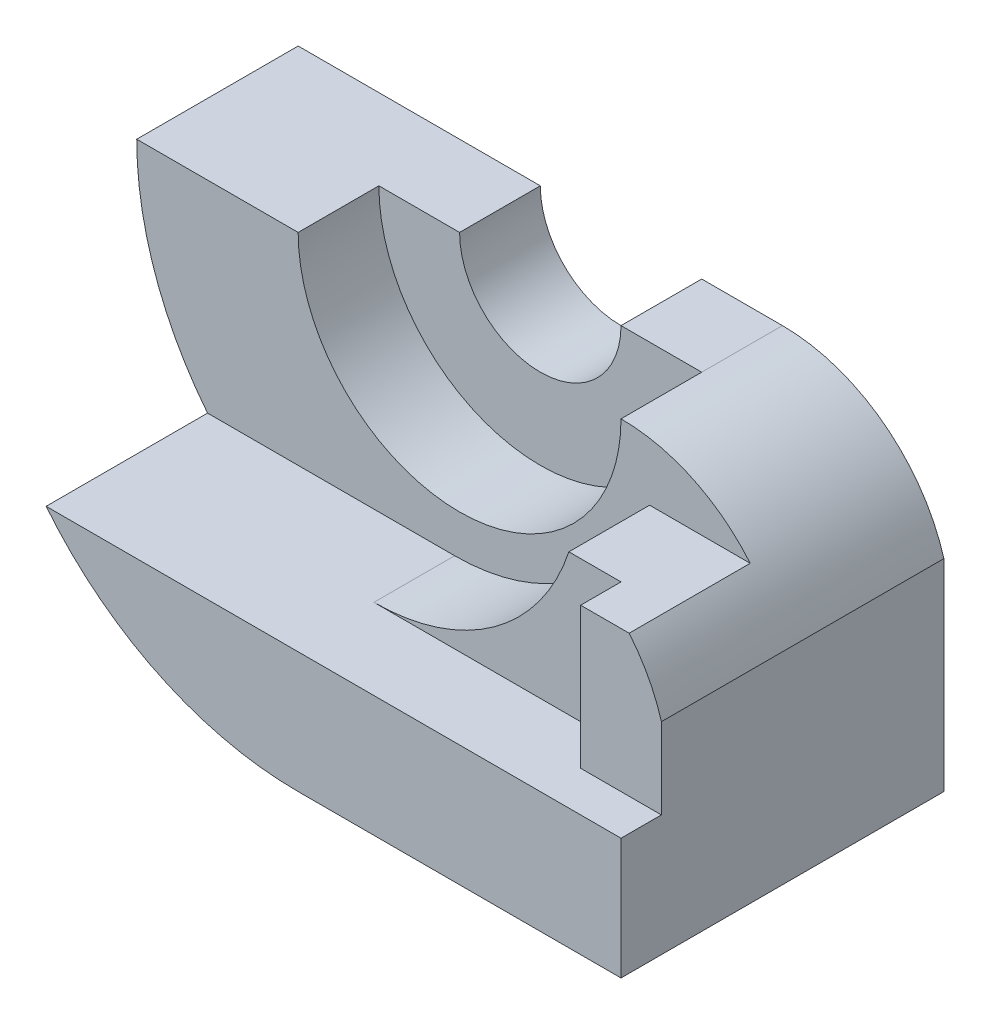
SolidWorks part; units mm, degrees
ref_plane "Front Plane" through (0, 0, 0) normal (0, 0, 1) x (1, 0, 0)
ref_plane "Top Plane" through (0, 0, 0) normal (0, 1, 0) x (1, 0, 0)
ref_plane "Right Plane" through (0, 0, 0) normal (1, 0, 0) x (0, 0, -1)
sketch "Sketch1" plane through (0, 0, 0) normal (0, 0, 1) x (1, 0, 0)
  line L0 (-40, 0) -> (-20, 0)
  line L1 (20, 0) -> (40, 0)
  line L2 (-80, 0) -> (-40, 0)
  line L3 (0, -80) -> (80, -80)
  line L4 (80, -80) -> (80, -30)
  arc A0 (20, 0) -> (-20, 0) centre (0, 0) cw
  arc A1 (40, 0) -> (-40, 0) centre (0, 0) cw
  arc A2 (-80, 0) -> (0, -80) centre (0, 0) ccw
  arc A3 (80, -30) -> (40, 0) centre (40, -41.6667) ccw
  dimension "D1" = 20
  dimension "D2" = 40
  dimension "D3" = 80
  dimension "D4" = 40
  dimension "D5" = 20
  dimension "D7" = 80
  dimension "D8" = 50
extrude "Boss-Extrude5" add sketch "Sketch1" along normal blind 80 contours L4 A3 A1 L2 A2 L3
sketch "Sketch4" plane through (0, 0, 0) normal (0, 0, -1) x (-1, 0, 0)
  line L0 (-20, 0) -> (-40, 0)
  line L1 (20, 0) -> (40, 0)
  line L5 (-80, -30) -> (-80, -80)
  line L6 (-80, -80) -> (0, -80)
  line L7 (80, 0) -> (40, 0)
  line L8 (-80, -30) -> (-80, -80)
  line L9 (-80, -80) -> (0, -80)
  line L10 (80, 0) -> (40, 0)
  arc A0 (20, 0) -> (-20, 0) centre (0, 0) cw
  arc A1 (40, 0) -> (-40, 0) centre (0, 0) cw
  arc A2 (-40, 0) -> (40, 0) centre (0, 0) ccw construction
  arc A4 (0, -80) -> (80, 0) centre (0, 0) ccw
  arc A5 (-40, 0) -> (40, 0) centre (0, 0) ccw
  arc A6 (-40, 0) -> (-80, -30) centre (-40, -41.6667) ccw
  arc A7 (0, -80) -> (80, 0) centre (0, 0) ccw
  arc A9 (-40, 0) -> (-80, -30) centre (-40, -41.6667) ccw
  arc M11 (40, 0) -> (-40, 0) centre (0, 0) cw
  dimension "D1" = 20
  dimension "D3" = 40
  dimension "D4" = 20
  dimension "D5" = 60
  dimension "D2" = 0
extrude "Boss-Extrude6" add sketch "Sketch4" against normal blind 20 contours L1 A0 L0 M11
ref_plane "Plane1" through (-80, 0, 0) normal (1, 0, 0) x (0, 0, -1)
sketch "Sketch6" plane through (-80, 0, 0) normal (1, 0, 0) x (0, 0, -1)
  line L1 (-80, 0) -> (-70, 0)
  line L2 (-80, 0) -> (-80, -50)
  line L3 (-80, -50) -> (-70, -50)
  line L4 (-70, 0) -> (-70, -50)
  dimension "D1" = 10
  dimension "D2" = 30
extrude "Cut-Extrude5" cut sketch "Sketch6" along normal blind 222
sketch "Sketch7" plane through (-80, 0, 0) normal (1, 0, 0) x (0, 0, -1)
  line L1 (-70, 0) -> (-40, 0)
  line L2 (-70, 0) -> (-70, -15)
  line L3 (-70, -15) -> (-40, -15)
  line L4 (-40, 0) -> (-40, -15)
  dimension "D1" = 15
  dimension "D2" = 30
extrude "Cut-Extrude6" cut sketch "Sketch7" along normal blind 222
sketch "Sketch9" plane through (0, 0, 70) normal (0, 0, 1) x (1, 0, 0)
  line L0 (60, -15) -> (60, -50)
  line L1 (72.0156, -15) -> (37.081, -15) construction
  line L2 (80, -50) -> (-62.45, -50) construction
  line L3 (60, -50) -> (80, -50)
  line L4 (80, -50) -> (80, -30)
  line L9 (72.0156, -15) -> (37.081, -15)
  line L10 (-37.081, -15) -> (-78.5812, -15)
  line L11 (-62.45, -50) -> (80, -50)
  line L12 (80, -50) -> (80, -30)
  line L13 (60, -15) -> (37.081, -15)
  line L14 (-37.081, -15) -> (-78.5812, -15)
  line L15 (-62.45, -50) -> (80, -50)
  line L16 (80, -50) -> (80, -30)
  arc A0 (80, -30) -> (72.0156, -15) centre (40, -41.6667) ccw
  arc A1 (80, -30) -> (72.0156, -15) centre (40, -41.6667) ccw construction
  arc A5 (80, -30) -> (72.0156, -15) centre (40, -41.6667) ccw
  arc A6 (-37.081, -15) -> (37.081, -15) centre (0, 0) ccw
  arc A7 (-78.5812, -15) -> (-62.45, -50) centre (0, 0) ccw
  arc A8 (80, -30) -> (72.0156, -15) centre (40, -41.6667) ccw
  arc A9 (-37.081, -15) -> (37.081, -15) centre (0, 0) ccw
  arc A10 (-78.5812, -15) -> (-62.45, -50) centre (0, 0) ccw
  arc M8 (80, -30) -> (72.0156, -15) centre (40, -41.6667) ccw
  line M9 (72.0156, -15) -> (37.081, -15)
  line M13 (-62.45, -50) -> (80, -50)
  line M14 (80, -50) -> (80, -30)
  dimension "D1" = 20
  dimension "D2" = 34.9346
  dimension "D3" = 0
extrude "Cut-Extrude7" cut sketch "Sketch9" against normal blind 10 contours L0 M9 M13 M14 M8
sketch "Sketch10" plane through (0, 0, 70) normal (0, 0, 1) x (1, 0, 0)
  line L0 (60, -50) -> (60, -15)
  line L2 (60, -15) -> (47.081, -15)
  line L3 (60, -15) -> (37.081, -15) construction
  line L4 (60, -50) -> (-62.45, -50) construction
  line L5 (60, -50) -> (-1.225, -50)
  arc A0 (-20, 0) -> (20, 0) centre (0, 0) ccw construction
  arc A1 (-20, 0) -> (20, 0) centre (0, 0) ccw construction
  arc A2 (-1.225, -50) -> (47.081, -15) centre (-1.225, 0.8353) ccw
  point P19 (0, -20)
  dimension "D4" = 60
  dimension "D1" = 0
  dimension "D2" = 10
  dimension "D3" = 35
extrude "Cut-Extrude8" cut sketch "Sketch10" against normal blind 10
sketch "Sketch11" plane through (0, 0, 60) normal (0, 0, 1) x (1, 0, 0)
  line L0 (80, -50) -> (80, -30)
  line L1 (80, -50) -> (60, -50)
  line L2 (-1.225, -50) -> (80, -50) construction
  line L3 (60, -50) -> (60, -15)
  line L4 (72.0156, -15) -> (47.081, -15) construction
  line L5 (60, -15) -> (70, -15)
  line L9 (72.0156, -15) -> (47.081, -15)
  line L10 (-1.225, -50) -> (80, -50)
  line L11 (80, -50) -> (80, -30)
  line L12 (70, -15) -> (47.081, -15)
  line L13 (-1.225, -50) -> (80, -50)
  line L14 (80, -50) -> (80, -30)
  arc A0 (80, -30) -> (72.0156, -15) centre (40, -41.6667) ccw
  arc A1 (80, -30) -> (72.0156, -15) centre (40, -41.6667) ccw construction
  arc A4 (-1.225, -50) -> (47.081, -15) centre (-1.225, 0.8353) ccw
  arc A5 (80, -30) -> (72.0156, -15) centre (40, -41.6667) ccw
  arc A6 (-1.225, -50) -> (47.081, -15) centre (-1.225, 0.8353) ccw
  arc A7 (80, -30) -> (72.0156, -15) centre (40, -41.6667) ccw
  dimension "D1" = 20
  dimension "D2" = 10
  dimension "D3" = 0
extrude "Boss-Extrude9" add sketch "Sketch11" along normal blind 10 contours L3 L13 L14 A7 L12
sketch "Sketch15" plane through (0, 0, 70) normal (0, 0, 1) x (1, 0, 0)
  line L0 (47.081, -15) -> (37.081, -15) construction
  line L1 (47.081, -15) -> (37.081, -15)
  line L2 (-62.45, -50) -> (-1.225, -50)
  line L3 (-78.5812, -15) -> (-37.081, -15)
  arc A0 (-1.225, -50) -> (47.081, -15) centre (-1.225, 0.8353) ccw
  arc A1 (-1.225, -50) -> (47.081, -15) centre (-1.225, 0.8353) ccw construction
  arc A2 (-78.5812, -15) -> (-62.45, -50) centre (0, 0) ccw
  arc A3 (-37.081, -15) -> (37.081, -15) centre (0, 0) ccw
extrude "Cut-Extrude14" cut sketch "Sketch15" against normal blind 30
